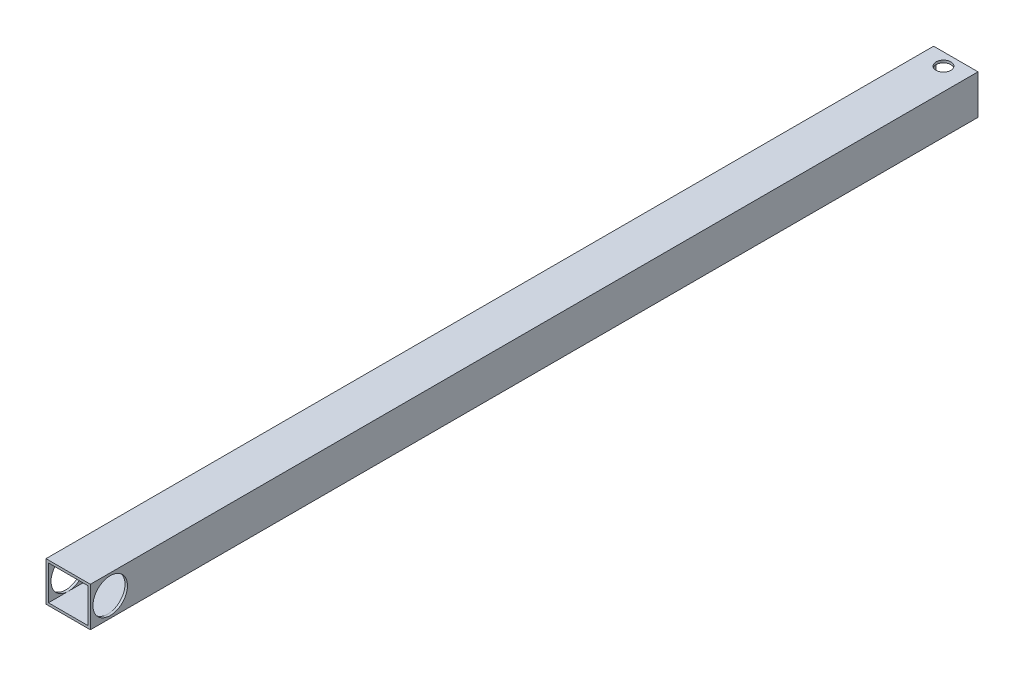
SolidWorks part; units mm, degrees
ref_plane "Front Plane" through (0, 0, 0) normal (0, 0, 1) x (1, 0, 0)
ref_plane "Top Plane" through (0, 0, 0) normal (0, 1, 0) x (1, 0, 0)
ref_plane "Right Plane" through (0, 0, 0) normal (1, 0, 0) x (0, 0, -1)
sketch "Sketch2" plane through (0, 0, 0) normal (0, 0, 1) x (1, 0, 0)
  line L1 (-4.5, 4) -> (4.5, 4)
  line L2 (-4.5, 4) -> (-4.5, -4)
  line L3 (-4.5, -4) -> (4.5, -4)
  line L4 (4.5, 4) -> (4.5, -4)
  line L5 (-4.5, 4) -> (4.5, -4) construction
  line L6 (-4.5, -4) -> (4.5, 4) construction
  point P0 (0, 0)
  dimension "D1" = 8
  dimension "D2" = 9
extrude "Boss-Extrude1" add sketch "Sketch2" along normal blind 180
sketch "Sketch3" plane through (0, 4, 0) normal (0, 1, 0) x (1, 0, 0)
  line L0 (-4.5, 0) -> (-4.5, -5.0008) construction
  line L1 (-4.5, -180) -> (-4.5, 0) construction
  line L2 (4.5, -5.0008) -> (-4.5, 0) construction
  line L3 (4.5, -180) -> (4.5, 0) construction
  line L4 (4.5, 0) -> (-4.5, -5.0008) construction
  line L5 (-4.5, -5.0008) -> (-4.4614, -4.9714) construction
  circle A0 centre (0, -2.5004) radius 1.5
  dimension "D1" = 3
extrude "Cut-Extrude1" cut sketch "Sketch3" against normal through all
sketch "Sketch4" plane through (0, 0, 0) normal (0, 0, 1) x (1, 0, 0)
  line L1 (-4, 3.5) -> (4, 3.5)
  line L2 (-4, 3.5) -> (-4, -3.5)
  line L3 (-4, -3.5) -> (4, -3.5)
  line L4 (4, 3.5) -> (4, -3.5)
  line L5 (-4, 3.5) -> (4, -3.5) construction
  line L6 (-4, -3.5) -> (4, 3.5) construction
  point P0 (0, 0)
  dimension "D1" = 7
  dimension "D2" = 8
extrude "Cut-Extrude2" cut sketch "Sketch4" along normal through all
sketch "Sketch5" plane through (4.5, 0, 0) normal (1, 0, 0) x (0, 0, -1)
  line L0 (-180, 4) -> (-171.961, 4) construction
  line L1 (-180, 4) -> (0, 4) construction
  line L2 (-171.961, 4) -> (-171.961, -4) construction
  line L3 (-180, -4) -> (0, -4) construction
  line L4 (-171.961, -4) -> (-180, 4) construction
  line L5 (-171.961, 4) -> (-180, -4) construction
  line L6 (-180, -4) -> (-179.9734, -3.9989) construction
  circle A0 centre (-175.9805, 0) radius 3.5
  dimension "D1" = 7
extrude "Cut-Extrude3" cut sketch "Sketch5" against normal through all
